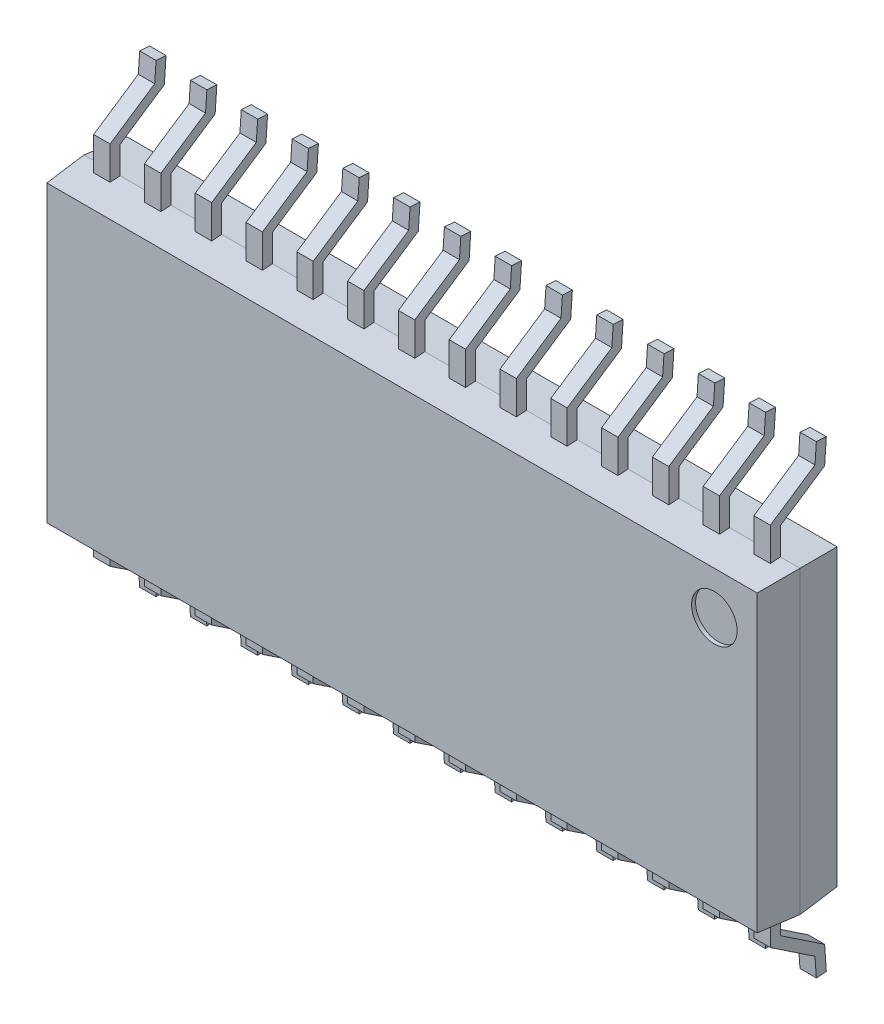
SolidWorks part; units mm, degrees
ref_plane "Front Plane" through (0, 0, 0) normal (0, 0, 1) x (1, 0, 0)
ref_plane "Top Plane" through (0, 0, 0) normal (0, 1, 0) x (1, 0, 0)
ref_plane "Right Plane" through (0, 0, 0) normal (1, 0, 0) x (0, 0, -1)
sketch "Sketch1" plane through (0, 0, 0) normal (0, 0, 1) x (1, 0, 0)
  line L1 (0, 0) -> (17.9, 0)
  line L2 (0, 0) -> (0, 7.5)
  line L3 (0, 7.5) -> (17.9, 7.5)
  line L4 (17.9, 0) -> (17.9, 7.5)
  dimension "D1" = 17.9
  dimension "D2" = 7.5
extrude "Boss-Extrude1" add sketch "Sketch1" along normal blind 1 draft 4
sketch "Sketch2" plane through (0, 0, 0) normal (0, 0, -1) x (-1, 0, 0)
  line L1 (-17.9, 7.5) -> (0, 7.5)
  line L2 (-17.9, 7.5) -> (-17.9, 0)
  line L3 (-17.9, 0) -> (0, 0)
  line L4 (0, 7.5) -> (0, 0)
extrude "Boss-Extrude2" add sketch "Sketch2" along normal blind 1 draft 4 separate body
ref_plane "Plane1" through (0.695, 0, 0) normal (1, 0, 0) x (0, 0, -1)
sketch "Sketch3" plane through (0.695, 0, 0) normal (1, 0, 0) x (0, 0, -1)
  line L0 (0, 0) -> (0, -0.7)
  line L1 (0, -0.7) -> (1.1074, -1.4404)
  line L2 (1.1074, -1.4404) -> (1.15, -2.05)
  line L3 (1.1074, -1.4404) -> (1.1074, -4.872) construction
  line L4 (1, 7.4301) -> (1, 0.0699) construction
  dimension "D1" = 2.05
  dimension "D2" = 0.6096
  dimension "D3" = 4
  dimension "D4" = 0.15
  dimension "D5" = 0.7
extrude "Extrude-Thin3" add sketch "Sketch3" along normal mid plane 0.41 separate body thin
pattern_linear "LPattern1" count 14 spacing 1.27 along (1, 0, 0) of "Extrude-Thin3"
ref_plane "Plane2" through (0, 3.74, 0) normal (0, 1, 0) x (1, 0, 0)
mirror "Mirror3" about plane through (0, 3.74, 0) normal (0, 1, 0) of "Extrude-Thin3", "LPattern1"
sketch "Sketch4" plane through (0, 0, 1) normal (0, 0, 1) x (1, 0, 0)
  line L0 (17.9, 0) -> (17.9, 7.5) construction
  line L1 (17.9, 7.5) -> (17.41, 7.5) construction
  circle A0 centre (16.76, 6.36) radius 0.57
  dimension "D1" = 1.14
  dimension "D2" = 1.14
  dimension "D3" = 1.14
extrude "Cut-Extrude1" cut sketch "Sketch4" against normal blind 0.1
